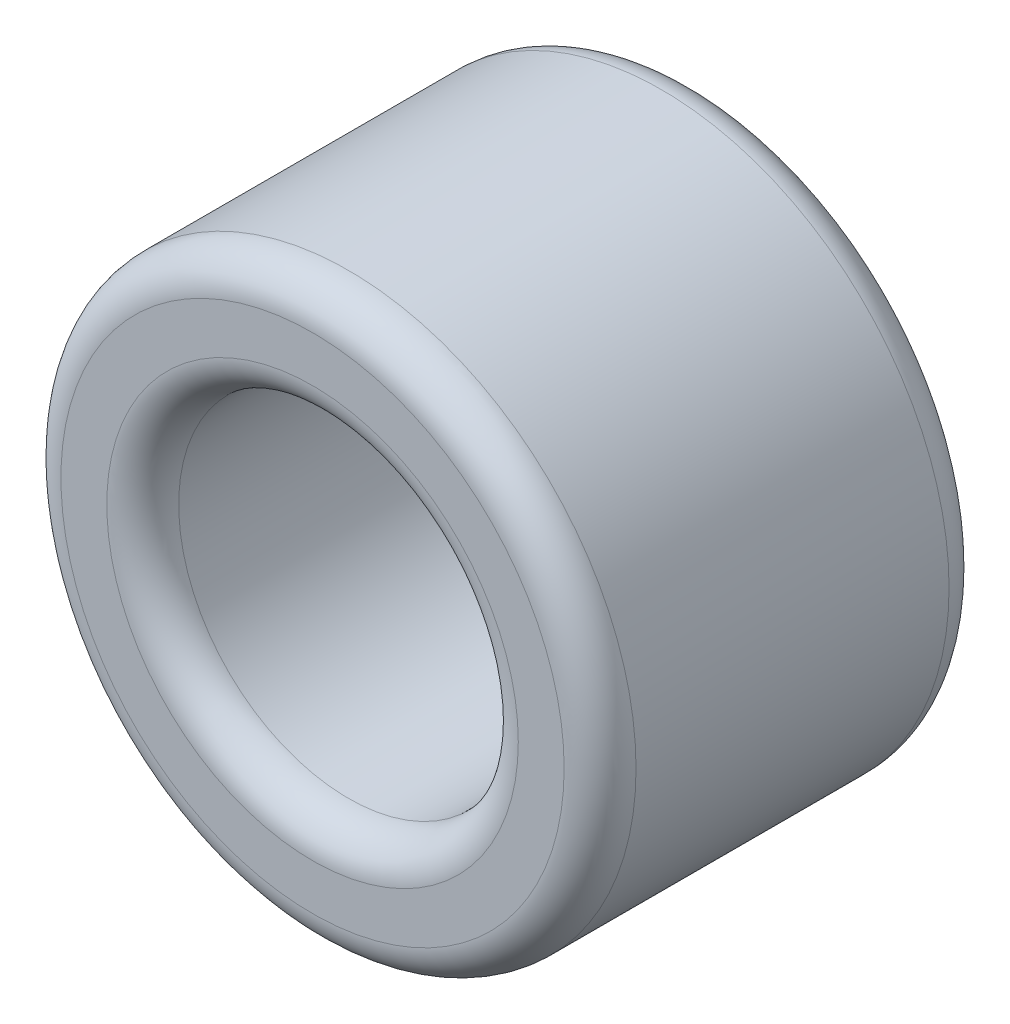
SolidWorks part; units mm, degrees
ref_plane "Front Plane" through (0, 0, 0) normal (0, 0, 1) x (1, 0, 0)
ref_plane "Top Plane" through (0, 0, 0) normal (0, 1, 0) x (1, 0, 0)
ref_plane "Right Plane" through (0, 0, 0) normal (1, 0, 0) x (0, 0, -1)
sketch "Sketch1" plane through (0, 0, 0) normal (0, 0, 1) x (1, 0, 0)
  circle A0 centre (0, 0) radius 127
  dimension "D1" = 254
extrude "Boss-Extrude1" add sketch "Sketch1" along normal blind 170
sketch "Sketch2" plane through (0, 0, 170) normal (0, 0, 1) x (1, 0, 0)
  circle A0 centre (0, 0) radius 75
  dimension "D1" = 150
extrude "Cut-Extrude1" cut sketch "Sketch2" against normal through all
fillet "Fillet1" radius 15.875 4 edges at (75, 0, 170) (75, 0, 0) (127, 0, 0) (127, 0, 170)
